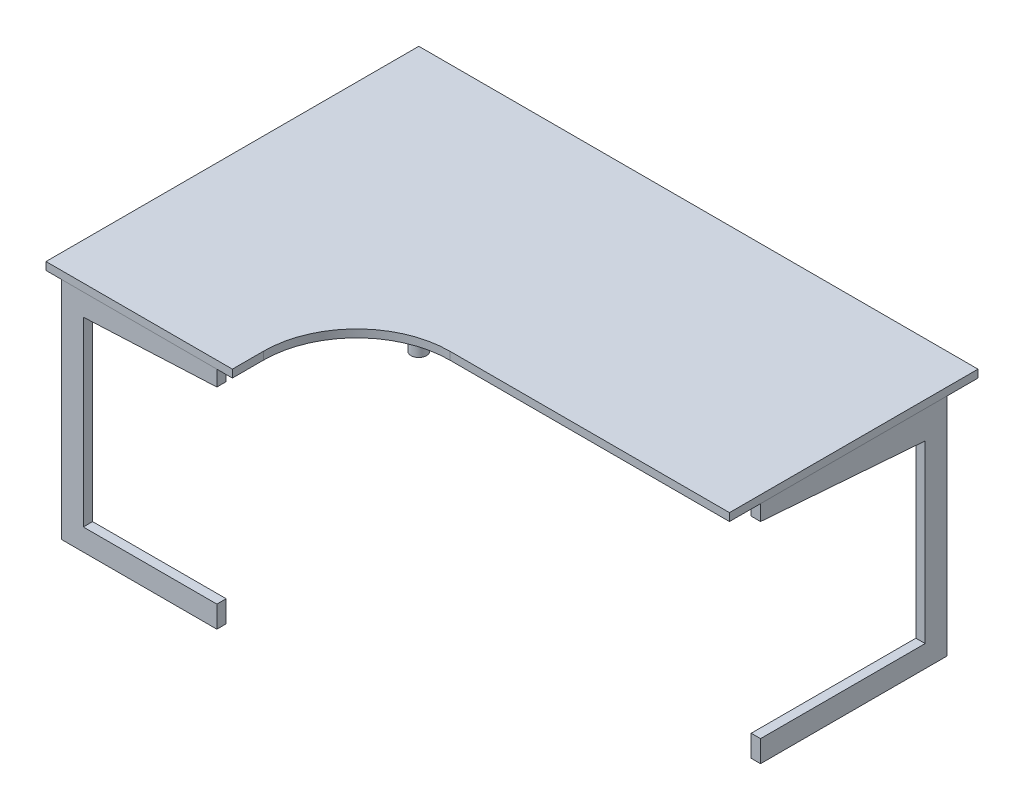
SolidWorks part; units mm, degrees
ref_plane "Front Plane" through (0, 0, 0) normal (0, 0, 1) x (1, 0, 0)
ref_plane "Top Plane" through (0, 0, 0) normal (0, 1, 0) x (1, 0, 0)
ref_plane "Right Plane" through (0, 0, 0) normal (1, 0, 0) x (0, 0, -1)
sketch "Sketch1" plane through (0, 0, 0) normal (1, 0, 0) x (0, 0, -1)
  line L0 (0, 0) -> (-600, 0)
  line L1 (-600, 0) -> (-600, 70)
  line L2 (-600, 70) -> (-70, 70)
  line L3 (-70, 70) -> (-70, 635)
  line L4 (-70, 635) -> (-600, 675)
  line L5 (-600, 675) -> (-600, 725)
  line L6 (-600, 725) -> (0, 725)
  line L7 (0, 725) -> (0, 0)
  dimension "D1" = 725
  dimension "D2" = 600
  dimension "D3" = 70
  dimension "D4" = 70
  dimension "D5" = 50
  dimension "D6" = 600
  dimension "D7" = 90
extrude "Extrude1" add sketch "Sketch1" against normal blind 30
sketch "Sketch2" plane through (0, 725, 0) normal (0, 1, 0) x (-1, 0, 0)
  line L0 (0, 700) -> (900, 700)
  line L1 (0, -100) -> (1800, -100)
  line L2 (0, -100) -> (0, 700)
  line L3 (1800, 1100) -> (1200, 1100)
  line L4 (1800, -100) -> (1800, 1100)
  line L5 (1200, 1100) -> (1200, 1000)
  arc A0 (900, 700) -> (1200, 1000) centre (900, 1000) ccw
  dimension "D6" = 300
  dimension "D1" = 1800
  dimension "D2" = 1200
  dimension "D3" = 100
  dimension "D4" = 800
  dimension "D5" = 600
extrude "Extrude2" add sketch "Sketch2" along normal blind 25 separate body
sketch "Sketch3" plane through (0, 0, 1100) normal (0, 0, 1) x (1, 0, 0)
  line L0 (-1750, 725) -> (-1750, 0)
  line L2 (-1750, 0) -> (-1250, 0)
  line L3 (-1250, 0) -> (-1250, 70)
  line L4 (-1250, 70) -> (-1680, 70)
  line L5 (-1680, 70) -> (-1680, 655)
  line L6 (-1680, 655) -> (-1250, 675)
  line L7 (-1250, 675) -> (-1250, 725)
  line L8 (-1250, 725) -> (-1750, 725)
  line L9 (-1800, 725) -> (-1200, 725) construction
  dimension "D1" = 50
  dimension "D2" = 70
  dimension "D3" = 70
  dimension "D4" = 50
  dimension "D5" = 70
  dimension "D6" = 500
  dimension "D7" = 500
extrude "Extrude3" add sketch "Sketch3" against normal blind 30 separate body
sketch "Sketch5" plane through (0, 0, 0) normal (0, 1, 0) x (1, 0, 0)
  line L1 (-30, 0) -> (0, 0) construction
  line L2 (-1800, 100) -> (-1800, -1100) construction
  circle A0 centre (-1700, 0) radius 25
  dimension "D1" = 50
  dimension "D2" = 100
extrude "Extrude4" add sketch "Sketch5" along normal up to surface (725 mm away) up to face at (-994.5903, 725, 619.6954)
